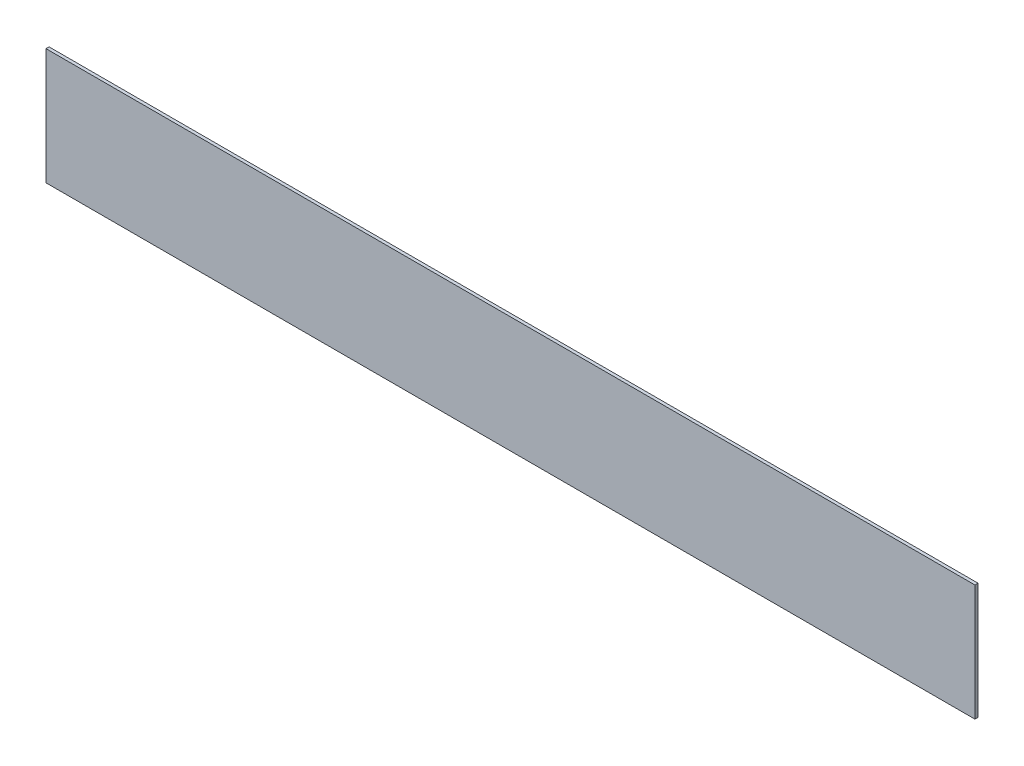
SolidWorks part; units mm, degrees
material "Acrílico (médio-alto impacto)"
ref_plane "Plano frontal" through (0, 0, 0) normal (0, 0, 1) x (1, 0, 0)
ref_plane "Plano superior" through (0, 0, 0) normal (0, 1, 0) x (1, 0, 0)
ref_plane "Plano direito" through (0, 0, 0) normal (1, 0, 0) x (0, 0, -1)
sketch "Esboço1" plane through (0, 0, 0) normal (0, 0, 1) x (1, 0, 0)
  line L1 (-599.5, -75) -> (599.5, -75)
  line L2 (-599.5, -75) -> (-599.5, 75)
  line L3 (-599.5, 75) -> (599.5, 75)
  line L4 (599.5, -75) -> (599.5, 75)
  line L5 (-599.5, -75) -> (599.5, 75) construction
  line L6 (-599.5, 75) -> (599.5, -75) construction
  point P0 (0, 0)
  dimension "D1" = 1199
  dimension "D2" = 150
extrude "Ressalto-extrusão1" add sketch "Esboço1" along normal blind 4
